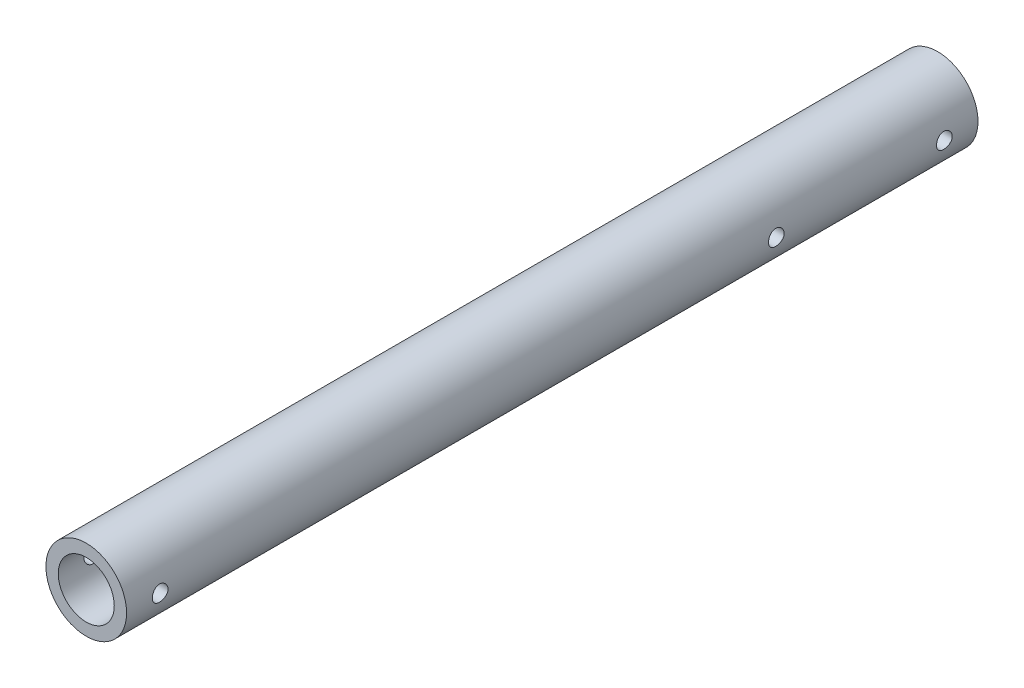
SolidWorks part; units mm, degrees
material "ﾎﾟﾘ塩化ﾋﾞﾆﾙ(PVC)硬質"
ref_plane "正面(Front)" through (0, 0, 0) normal (0, 0, 1) x (1, 0, 0)
ref_plane "平面(Top)" through (0, 0, 0) normal (0, 1, 0) x (1, 0, 0)
ref_plane "右側面(Right)" through (0, 0, 0) normal (1, 0, 0) x (0, 0, -1)
sketch "ｽｹｯﾁ1" plane through (0, 0, 0) normal (0, 0, 1) x (1, 0, 0)
  circle A0 centre (0, 0) radius 9
  circle A1 centre (0, 0) radius 6.25
  dimension "D1" = 18
  dimension "D2" = 12.5
extrude "ﾎﾞｽ - 押し出し1" add sketch "ｽｹｯﾁ1" along normal blind 190
sketch "ｽｹｯﾁ2" plane through (0, 0, 0) normal (1, 0, 0) x (0, 0, -1)
  line L0 (0, 0) -> (-231.2557, 0) construction
  line L1 (0, -9) -> (0, 9) construction
  line L2 (-190, 9) -> (-190, -9) construction
  circle A0 centre (-7.5, 0) radius 1.75
  circle A1 centre (-182.5, 0) radius 1.75
  circle A2 centre (-45, 0) radius 1.75
  dimension "D2" = 7.5
  dimension "D3" = 3.5
  dimension "D4" = 3.5
  dimension "D5" = 45
  dimension "D1" = 7.5
extrude "ｶｯﾄ - 押し出し1" cut sketch "ｽｹｯﾁ2" against normal through all both and the other way through all
